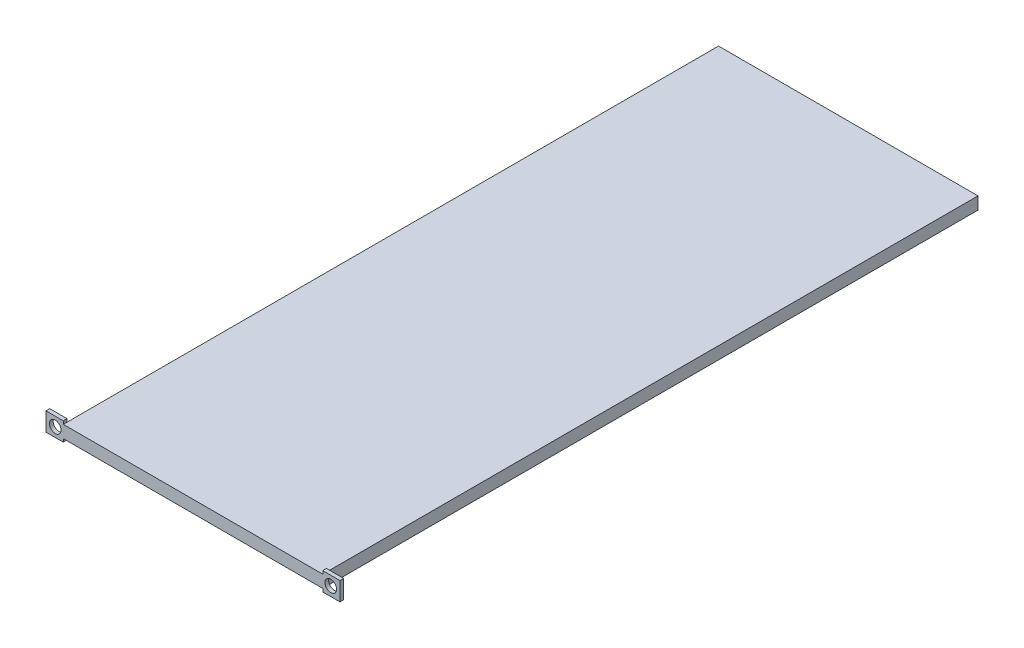
SolidWorks part; units mm, degrees
ref_plane "Front Plane" through (0, 0, 0) normal (0, 0, 1) x (1, 0, 0)
ref_plane "Top Plane" through (0, 0, 0) normal (0, 1, 0) x (1, 0, 0)
ref_plane "Right Plane" through (0, 0, 0) normal (1, 0, 0) x (0, 0, -1)
sketch "Sketch1" plane through (0, 0, 0) normal (0, 0, 1) x (1, 0, 0)
  line L1 (0, 0) -> (210.28, 0)
  line L2 (0, 0) -> (0, 10)
  line L3 (0, 10) -> (210.28, 10)
  line L4 (210.28, 0) -> (210.28, 10)
  dimension "D1" = 210.28
  dimension "D2" = 10
extrude "Boss-Extrude1" add sketch "Sketch1" along normal blind 531
sketch "Sketch2" plane through (0, 0, 0) normal (-1, 0, 0) x (0, 0, 1)
  line L0 (531, 10) -> (531, 0) construction
  line L1 (531, 12.5) -> (528, 12.5)
  line L2 (531, 12.5) -> (531, -2.5)
  line L3 (531, -2.5) -> (528, -2.5)
  line L4 (528, 12.5) -> (528, -2.5)
  dimension "D1" = 3
  dimension "D2" = 15
  dimension "D3" = 2.5
extrude "Boss-Extrude2" add sketch "Sketch2" along normal blind 14
sketch "Sketch4" plane through (210.28, 0, 0) normal (1, 0, 0) x (0, 0, -1)
  line L1 (-531, 12.5) -> (-528, 12.5)
  line L2 (-531, 12.5) -> (-531, -2.5)
  line L3 (-531, -2.5) -> (-528, -2.5)
  line L4 (-528, 12.5) -> (-528, -2.5)
extrude "Boss-Extrude3" add sketch "Sketch4" along normal blind 14
sketch "Sketch3" plane through (0, 0, 528) normal (0, 0, -1) x (-1, 0, 0)
  line L0 (0, 10) -> (0, 0) construction
  line L1 (-105.14, 41.7978) -> (-105.14, -48.9522) construction
  circle A0 centre (6.5, 5) radius 4.7
  circle A2 centre (-216.78, 5) radius 4.7
  dimension "D1" = 9.4
  dimension "D2" = 6.5
  dimension "D3" = 5
extrude "Cut-Extrude1" cut sketch "Sketch3" against normal blind 13
